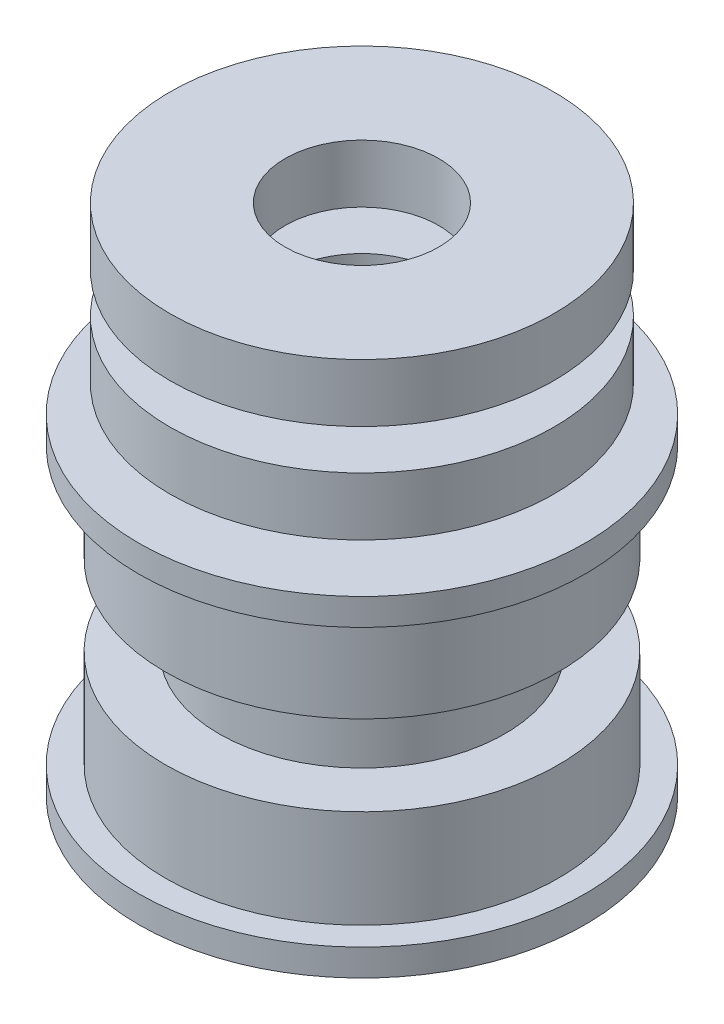
SolidWorks part; units mm, degrees
ref_plane "Front Plane" through (0, 0, 0) normal (0, 0, 1) x (1, 0, 0)
ref_plane "Top Plane" through (0, 0, 0) normal (0, 1, 0) x (1, 0, 0)
ref_plane "Right Plane" through (0, 0, 0) normal (1, 0, 0) x (0, 0, -1)
sketch "Sketch1" plane through (0, 0, 0) normal (0, 1, 0) x (1, 0, 0)
  circle A0 centre (0, 0) radius 12.5
  dimension "D1" = 25
extrude "Boss-Extrude1" add sketch "Sketch1" along normal blind 1.5
sketch "Sketch2" plane through (0, 1.5, 0) normal (0, 1, 0) x (1, 0, 0)
  circle A0 centre (0, 0) radius 11
  dimension "D1" = 22
extrude "Boss-Extrude2" add sketch "Sketch2" along normal blind 5.5
sketch "Sketch3" plane through (0, 7, 0) normal (0, 1, 0) x (1, 0, 0)
  circle A0 centre (0, 0) radius 8
  dimension "D1" = 16
extrude "Boss-Extrude3" add sketch "Sketch3" along normal blind 2.25
mirror "Mirror1" about plane through (0, 9.25, 0) normal (0, 1, 0) of bodies 108
sketch "Sketch4" plane through (0, 18.5, 0) normal (0, 1, 0) x (1, 0, 0)
  circle A0 centre (0, 0) radius 7.75
  dimension "D1" = 15.5
extrude "Boss-Extrude4" add sketch "Sketch4" along normal blind 1.5
sketch "Sketch5" plane through (0, 20, 0) normal (0, 1, 0) x (1, 0, 0)
  circle A0 centre (0, 0) radius 10.75
  dimension "D1" = 21.5
extrude "Boss-Extrude6" add sketch "Sketch5" along normal blind 3.25 contours A0
sketch "Sketch6" plane through (0, 0, 0) normal (0, -1, 0) x (1, 0, 0)
  circle A0 centre (0, 0) radius 4.3
  dimension "D1" = 8.6
sketch "Sketch10" plane through (0, 23.25, 0) normal (0, 1, 0) x (1, 0, 0)
  circle A0 centre (0, 0) radius 10.75
extrude "Boss-Extrude7" add sketch "Sketch10" along normal blind 3.25 from offset 2.25 separate body
extrude "Cut-Extrude2" cut sketch "Sketch6" against normal blind 50
